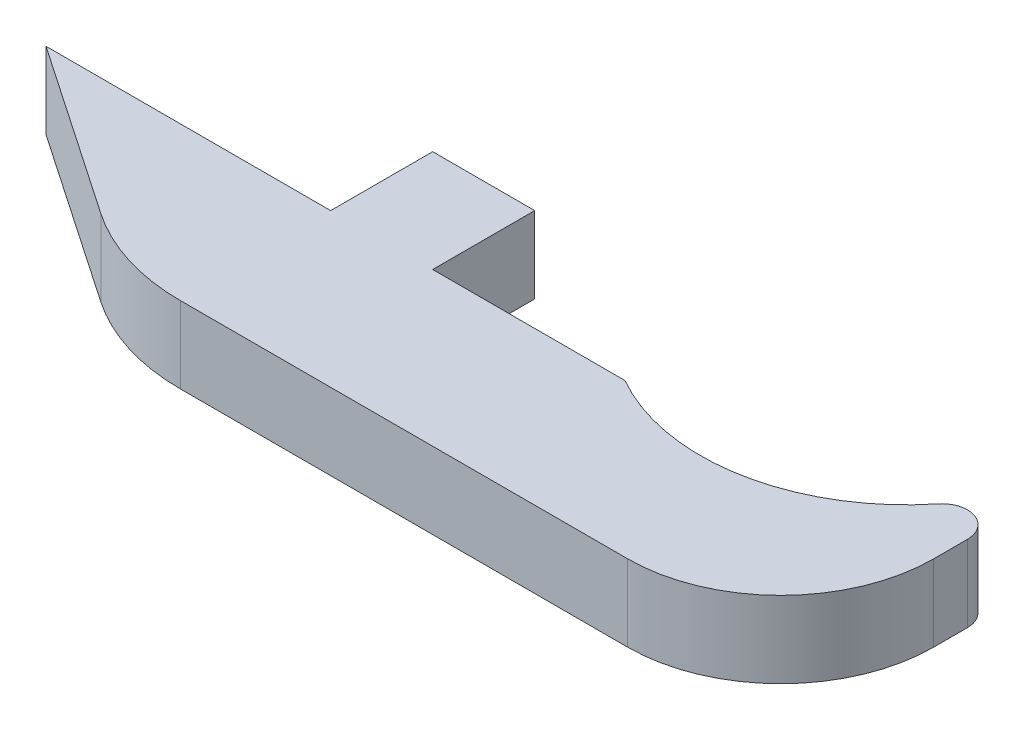
SolidWorks part; units mm, degrees
material "AISI 4130 Steel, annealed at 865C"
ref_plane "X-Y Datum" through (0, 0, 0) normal (0, 0, 1) x (1, 0, 0)
ref_plane "X-Z Datum" through (0, 0, 0) normal (0, 1, 0) x (1, 0, 0)
ref_plane "Y-Z Datum" through (0, 0, 0) normal (1, 0, 0) x (0, 0, -1)
sketch "Sketch1" plane through (0, 0, 0) normal (0, 1, 0) x (1, 0, 0)
  line L0 (20.5085, 0) -> (0, 0) construction
  line L1 (45.593, 0) -> (0, 0)
  line L2 (45.593, 0) -> (45.593, 11.1252)
  line L3 (17.145, -9.525) -> (58.42, -9.525)
  line L4 (58.42, 11.1252) -> (58.42, -9.525)
  line L5 (3.175, 0) -> (17.145, -9.525)
  circle A0 centre (45.593, 11.1252) radius 12.827
  dimension "D3" = 25.654
  dimension "D5" = 9.525
  dimension "D1" = 45.593
  dimension "D2" = 11.1252
  dimension "D4" = 3.175
  dimension "D6" = 41.275
extrude "Boss-Extrude1" add sketch "Sketch1" along normal blind 4.7625
fillet "Fillet1" radius 9.525 1 edges at (58.42, 2.3813, 9.525)
fillet "Fillet2" radius 1.5875 1 edges at (58.42, 2.3813, -11.1252)
fillet "Fillet4" radius 12.7 1 edges at (17.145, 2.3813, 9.525)
sketch "Sketch2" plane through (0, 0, 0) normal (0, -1, 0) x (1, 0, 0)
  line L1 (27.2395, -6.35) -> (27.2395, 0)
  line L2 (-7.0505, -6.35) -> (27.8745, -6.35) construction
  line L3 (27.2395, 0) -> (20.8895, 0)
  line L4 (27.2395, 0) -> (27.2395, -6.35)
  line L5 (27.2395, -6.35) -> (20.8895, -6.35)
  line L6 (20.8895, 0) -> (20.8895, -6.35)
  line L7 (33.5895, 0) -> (33.5895, -6.35) construction
  line M6 (3.175, 0) -> (39.2085, 0)
  dimension "D1" = 6.35
  dimension "D2" = 6.35
extrude "Boss-Extrude2" add sketch "Sketch2" against normal blind 4.7625 contours L6 L5 L1 M6
